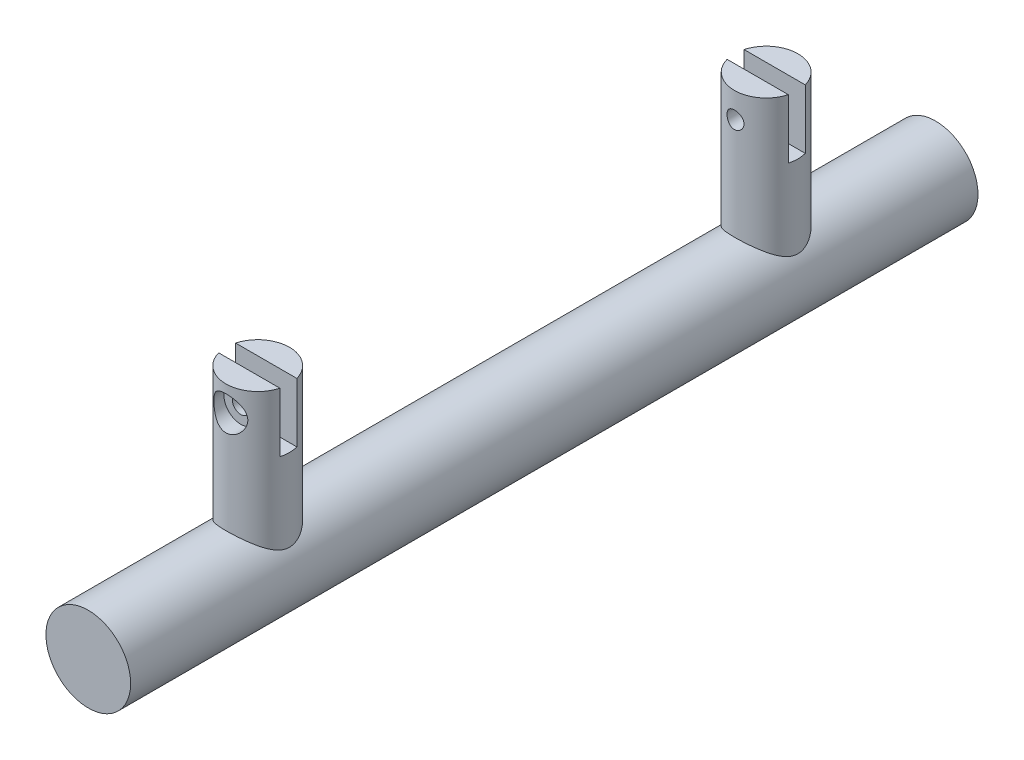
SolidWorks part; units mm, degrees
ref_plane "Front Plane" through (0, 0, 0) normal (0, 0, 1) x (1, 0, 0)
ref_plane "Top Plane" through (0, 0, 0) normal (0, 1, 0) x (1, 0, 0)
ref_plane "Right Plane" through (0, 0, 0) normal (1, 0, 0) x (0, 0, -1)
sketch "Sketch1" plane through (0, 0, 0) normal (0, 0, 1) x (1, 0, 0)
  circle A0 centre (0, 0) radius 10
  dimension "D1" = 20
extrude "Boss-Extrude1" add sketch "Sketch1" along normal mid plane 200 contours A0
sketch "Sketch2" plane through (0, 0, 0) normal (0, 1, 0) x (1, 0, 0)
  line L0 (15.6268, 0) -> (-16.6474, 0) construction
  circle A0 centre (0, 60) radius 7.5
  circle A1 centre (0, -60) radius 7.5
  dimension "D1" = 15
  dimension "D2" = 60
extrude "Boss-Extrude2" add sketch "Sketch2" along normal blind 40
sketch "Sketch3" plane through (0, 40, 0) normal (0, 1, 0) x (1, 0, 0)
  line L0 (0, 0) -> (-36.5158, 0) construction
  line L1 (-7.5, -58) -> (7.5, -58)
  line L2 (-7.5, -58) -> (-7.5, -62)
  line L3 (-7.5, -62) -> (7.5, -62)
  line L4 (7.5, -58) -> (7.5, -62)
  line L5 (-7.5, -58) -> (7.5, -62) construction
  line L6 (-7.5, -62) -> (7.5, -58) construction
  line L7 (0, 0) -> (0, -44.3553) construction
  line L8 (7.5, 58) -> (7.5, 62)
  line L9 (-7.5, 58) -> (7.5, 58)
  line L10 (-7.5, 62) -> (7.5, 62)
  line L11 (-7.5, 58) -> (-7.5, 62)
  point P0 (0, -60)
  dimension "D1" = 15
  dimension "D2" = 4
  dimension "D3" = 60
extrude "Cut-Extrude1" cut sketch "Sketch3" against normal blind 14
sketch "Sketch4" plane through (0, 0, 0) normal (0, 0, 1) x (1, 0, 0)
  line L0 (0, 0) -> (0, 19.8635) construction
  line L1 (7.2284, 40) -> (-7.2284, 40) construction
  circle A0 centre (0, 34) radius 2
  dimension "D2" = 4
  dimension "D1" = 6
extrude "Cut-Extrude2" cut sketch "Sketch4" against normal mid plane 140
sketch "Sketch5" plane through (0, 0, -100) normal (0, 0, -1) x (-1, 0, 0)
  circle A0 centre (0, 34) radius 4
  dimension "D1" = 8
extrude "Cut-Extrude3" cut sketch "Sketch5" against normal blind 36
sketch "Sketch6" plane through (0, 0, 100) normal (0, 0, 1) x (1, 0, 0)
  circle A0 centre (0, 34) radius 4
  dimension "D1" = 8
extrude "Cut-Extrude4" cut sketch "Sketch6" against normal blind 36
